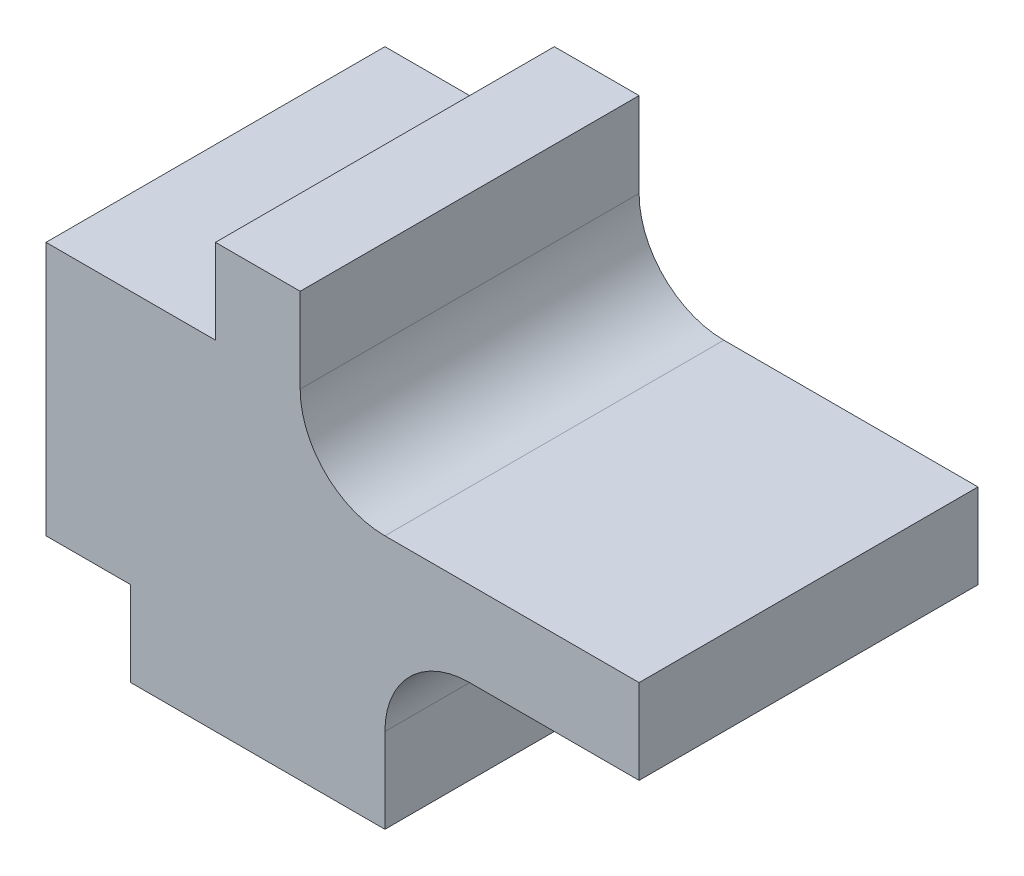
SolidWorks part; units mm, degrees
ref_plane "前基準面" through (0, 0, 0) normal (0, 0, 1) x (1, 0, 0)
ref_plane "上基準面" through (0, 0, 0) normal (0, 1, 0) x (1, 0, 0)
ref_plane "右基準面" through (0, 0, 0) normal (1, 0, 0) x (0, 0, -1)
sketch "草圖1" plane through (0, 0, 0) normal (0, 0, 1) x (1, 0, 0)
  line L0 (0, 0) -> (15, 0)
  line L1 (15, 0) -> (15, 5)
  line L2 (20, 10) -> (30, 10)
  line L3 (30, 10) -> (30, 15)
  line L4 (30, 15) -> (15, 15)
  line L5 (10, 20) -> (10, 25)
  line L6 (10, 25) -> (5, 25)
  line L7 (5, 25) -> (5, 20)
  line L8 (5, 20) -> (-5, 20)
  line L9 (-5, 20) -> (-5, 5)
  line L10 (-5, 5) -> (0, 5)
  line L11 (0, 5) -> (0, 0)
  arc A0 (15, 15) -> (10, 20) centre (15, 20) cw
  arc A1 (15, 5) -> (20, 10) centre (20, 5) cw
  point P10 (22.5, 15)
  point P14 (2.781, 45.2536)
  point P17 (10, 15)
  point P20 (15, 10)
  dimension "D11" = 5
  dimension "D1" = 5
  dimension "D2" = 15
  dimension "D3" = 10
  dimension "D4" = 35
  dimension "D5" = 5
  dimension "D6" = 5
  dimension "D7" = 20
  dimension "D8" = 25
  dimension "D9" = 15
  dimension "D10" = 5
extrude "填料-伸長1" add sketch "草圖1" along normal blind 20
